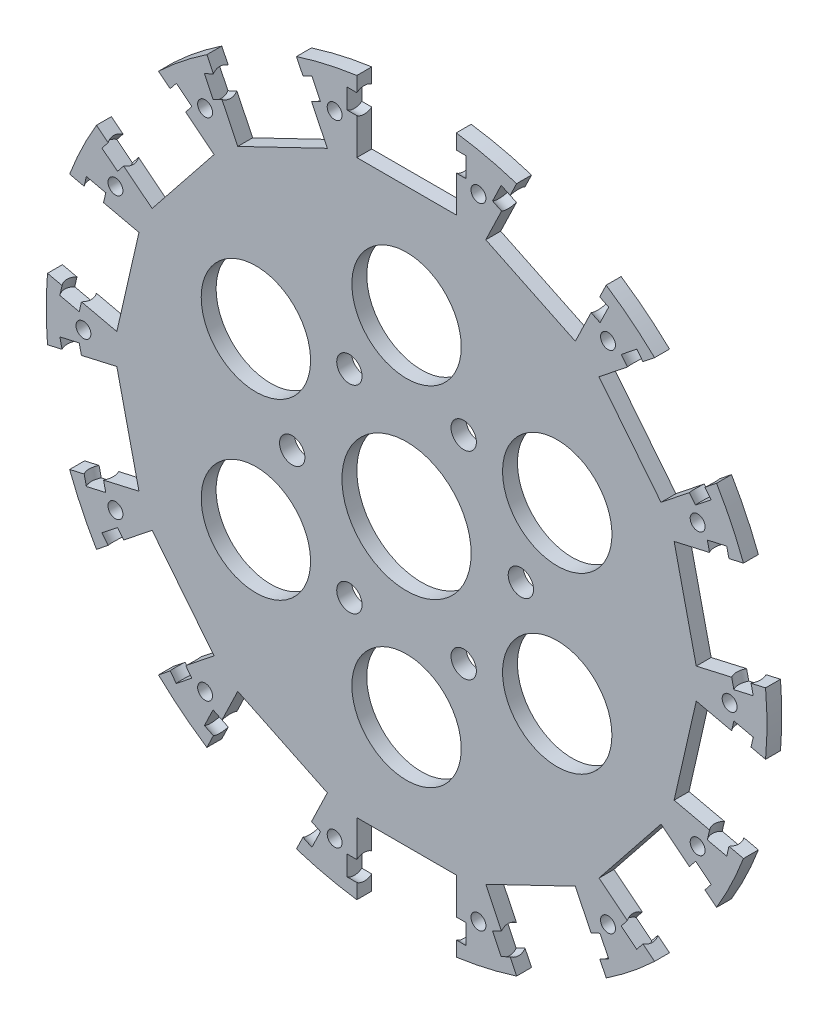
SolidWorks part; units mm, degrees
material "1060 合金"
ref_plane "前视基准面" through (0, 0, 0) normal (0, 0, 1) x (1, 0, 0)
ref_plane "上视基准面" through (0, 0, 0) normal (0, 1, 0) x (1, 0, 0)
ref_plane "右视基准面" through (0, 0, 0) normal (1, 0, 0) x (0, 0, -1)
sketch "草图1" plane through (0, 0, 0) normal (0, 0, 1) x (1, 0, 0)
  circle A0 centre (0, 0) radius 47.5
  dimension "D1" = 95
extrude "凸台-拉伸1" add sketch "草图1" along normal blind 3
sketch "草图2" plane through (0, 0, 3) normal (0, 0, 1) x (1, 0, 0)
  circle A0 centre (0, 0) radius 35 construction
  circle A1 centre (0, 35) radius 11
  dimension "D1" = 70
  dimension "D2" = 22
extrude "切除-拉伸1" cut sketch "草图2" against normal through all
sketch "草图3" plane through (0, 0, 3) normal (0, 0, 1) x (1, 0, 0)
  line L0 (0, 0) -> (11.5, 19.9186) construction
  line L1 (0, -29.6117) -> (0, 46) construction
  circle A0 centre (0, 0) radius 23 construction
  circle A1 centre (0, 35) radius 11 construction
  circle A2 centre (11.5, 19.9186) radius 2.55
  dimension "D1" = 46
  dimension "D3" = 5.1
  dimension "D2" = 30
pattern_circular "阵列(圆周)1" count 6 over 360 about axis through (0, 0, 0) along (0, 0, 1) of "切除-拉伸1"
extrude "切除-拉伸2" cut sketch "草图3" against normal through all
pattern_circular "阵列(圆周)2" count 6 over 360 about axis through (0, 0, 0) along (0, 0, 1) of "切除-拉伸2"
sketch "草图4" plane through (0, 0, 3) normal (0, 0, 1) x (1, 0, 0)
  circle A0 centre (0, 0) radius 13
  dimension "D1" = 26
extrude "切除-拉伸3" cut sketch "草图4" against normal through all
sketch "草图5" plane through (0, 0, 3) normal (0, 0, 1) x (1, 0, 0)
  circle A0 centre (0, 0) radius 72.5
  circle A1 centre (0, 0) radius 47.5
  dimension "D1" = 145
extrude "凸台-拉伸2" add sketch "草图5" against normal blind 3
sketch "草图6" plane through (0, 0, 0) normal (0, 0, -1) x (-1, 0, 0)
  line L0 (0, 0) -> (0, 72.5) construction
  line L1 (-10, 87.5) -> (10, 87.5)
  line L2 (-10, 87.5) -> (-10, 57.5)
  line L3 (-10, 57.5) -> (10, 57.5)
  line L4 (10, 87.5) -> (10, 57.5)
  line L5 (-10, 87.5) -> (10, 57.5) construction
  line L6 (-10, 57.5) -> (10, 87.5) construction
  circle A0 centre (0, 0) radius 72.5 construction
  point P0 (0, 72.5)
  dimension "D1" = 20
  dimension "D2" = 30
extrude "切除-拉伸4" cut sketch "草图6" against normal through all
pattern_circular "阵列(圆周)3" count 14 over 360 about axis through (0, 0, 0) along (0, 0, 1) of "切除-拉伸4"
sketch "草图7" plane through (0, 0, 3) normal (0, 0, 1) x (1, 0, 0)
  line L0 (0, 0) -> (-16.1328, 70.6823) construction
  circle A0 centre (0, 0) radius 65 construction
  arc A1 (-10, 71.807) -> (-22.1462, 69.0347) centre (0, 0) ccw construction
  circle A2 centre (-14.4639, 63.3703) radius 1.5
  dimension "D1" = 130
  dimension "D2" = 3
extrude "切除-拉伸5" cut sketch "草图7" against normal through all
pattern_circular "阵列(圆周)4" count 14 over 360 about axis through (0, 0, 0) along (0, 0, 1) of "切除-拉伸5"
sketch "草图8" plane through (9.0097, 4.3388, 0) normal (-0.901, -0.4339, 0) x (0, 0, 1)
  line L0 (1.5, 71.807) -> (1.5, 60.3571) construction
  line L1 (0, 71.807) -> (3, 71.807) construction
  line L2 (0, 60.3571) -> (3, 60.3571) construction
  circle A0 centre (1.5, 66.807) radius 2.5
  dimension "D2" = 5
  dimension "D1" = 5
extrude "切除-拉伸6" cut sketch "草图8" against normal blind 2
sketch "草图9" plane through (-10, 0, 0) normal (1, 0, 0) x (0, 0, -1)
  line L0 (-1.5, 71.807) -> (-1.5, 60.3571) construction
  line L1 (-3, 71.807) -> (0, 71.807) construction
  line L2 (-3, 60.3571) -> (0, 60.3571) construction
  circle A0 centre (-1.5, 66.807) radius 2.5
  dimension "D1" = 5
  dimension "D2" = 5
extrude "切除-拉伸7" cut sketch "草图9" against normal blind 2
pattern_circular "阵列(圆周)5" count 14 over 360 about axis through (0, 0, 0) along (0, 0, 1) of "切除-拉伸7", "切除-拉伸6"
